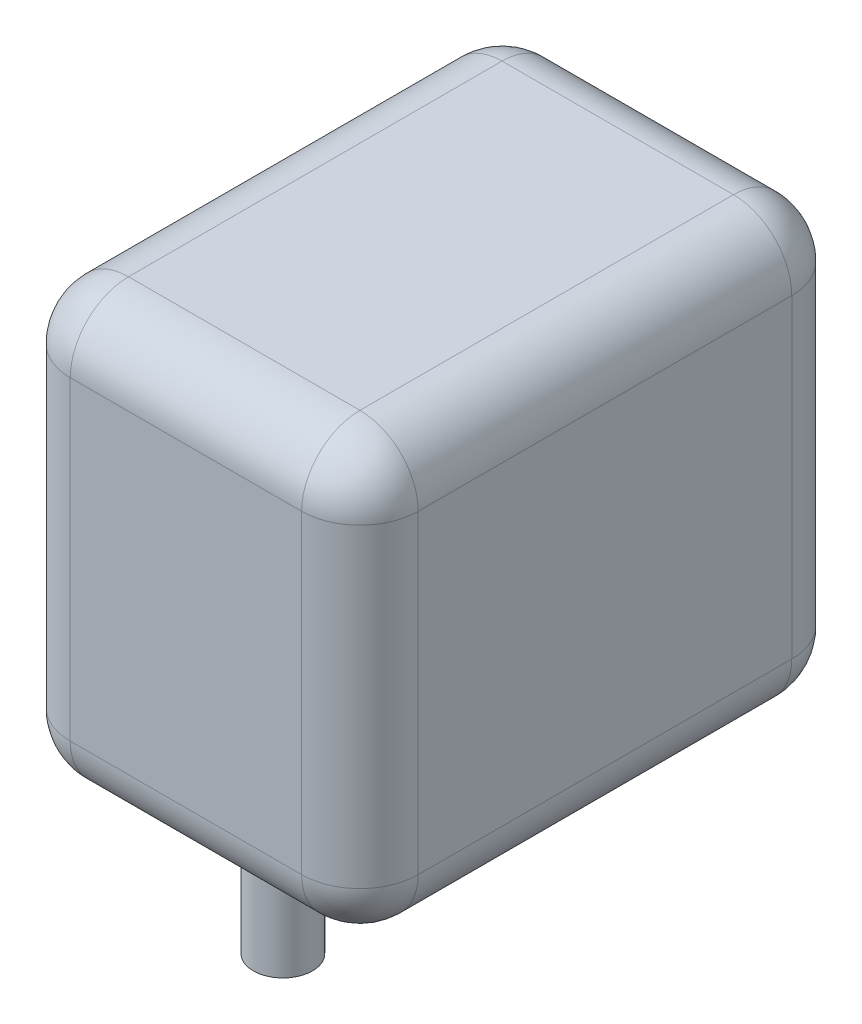
SolidWorks part; units mm, degrees
material "EPDM"
ref_plane "Front Plane" through (0, 0, 0) normal (0, 0, 1) x (1, 0, 0)
ref_plane "Top Plane" through (0, 0, 0) normal (0, 1, 0) x (1, 0, 0)
ref_plane "Right Plane" through (0, 0, 0) normal (1, 0, 0) x (0, 0, -1)
sketch "Sketch3" plane through (0, 0, 0) normal (0, 1, 0) x (1, 0, 0)
  line L1 (-29.845, 42.037) -> (29.845, 42.037)
  line L2 (-29.845, 42.037) -> (-29.845, -42.037)
  line L3 (-29.845, -42.037) -> (29.845, -42.037)
  line L4 (29.845, 42.037) -> (29.845, -42.037)
  line L5 (-29.845, 42.037) -> (29.845, -42.037) construction
  line L6 (-29.845, -42.037) -> (29.845, 42.037) construction
  point P0 (0, 0)
  dimension "D1" = 59.69
  dimension "D2" = 84.074
extrude "Boss-Extrude1" add sketch "Sketch3" along normal blind 93.98
sketch "Sketch4" plane through (0, 0, 0) normal (0, -1, 0) x (1, 0, 0)
  line L0 (-29.845, 42.037) -> (29.845, 42.037) construction
  line L1 (-29.845, -42.037) -> (-29.845, 42.037) construction
  line L2 (29.845, 42.037) -> (29.845, -42.037) construction
  line L3 (29.845, -42.037) -> (-29.845, -42.037) construction
  line L4 (-29.845, 42.037) -> (29.845, 42.037)
  line L5 (-29.845, -42.037) -> (-29.845, 42.037)
  line L6 (29.845, 42.037) -> (29.845, -42.037)
  line L7 (29.845, -42.037) -> (-29.845, -42.037)
  circle A0 centre (0, 25.4) radius 5.08
  line M1 (29.845, -42.037) -> (29.845, 42.037)
  line M2 (29.845, 42.037) -> (-29.845, 42.037)
  line M3 (-29.845, 42.037) -> (-29.845, -42.037)
  line M4 (-29.845, -42.037) -> (29.845, -42.037)
  dimension "D1" = 10.16
  dimension "D2" = 25.4
extrude "Cut-Extrude1" cut sketch "Sketch4" against normal blind 20 contours A0 M4 M1 M2 M3
fillet "Fillet1" radius 10 12 edges at (-29.845, 93.98, 0) (-29.845, 20, 0) (0, 93.98, -42.037) (-29.845, 56.99, -42.037) (0, 20, -42.037) (29.845, 93.98, 0) (29.845, 56.99, -42.037) (29.845, 20, 0) (-29.845, 56.99, 42.037) (0, 93.98, 42.037) (29.845, 56.99, 42.037) (0, 20, 42.037)
